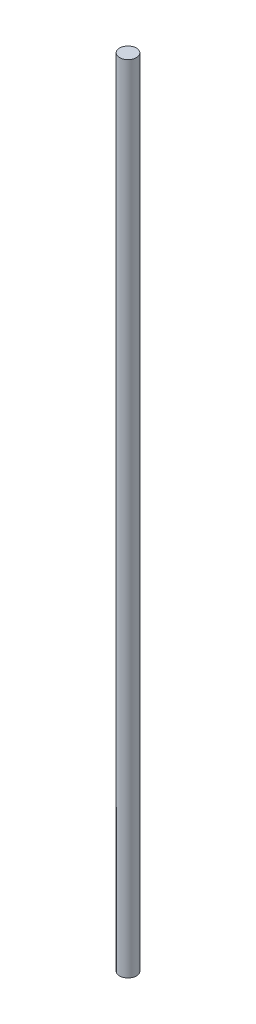
SolidWorks part; units mm, degrees
ref_plane "前视基准面" through (0, 0, 0) normal (0, 0, 1) x (1, 0, 0)
ref_plane "上视基准面" through (0, 0, 0) normal (0, 1, 0) x (1, 0, 0)
ref_plane "右视基准面" through (0, 0, 0) normal (1, 0, 0) x (0, 0, -1)
sketch "草图1" plane through (0, 0, 0) normal (0, 1, 0) x (1, 0, 0)
  circle A0 centre (0, 0) radius 5
  dimension "D1" = 10
extrude "凸台-拉伸1" add sketch "草图1" along normal blind 475
